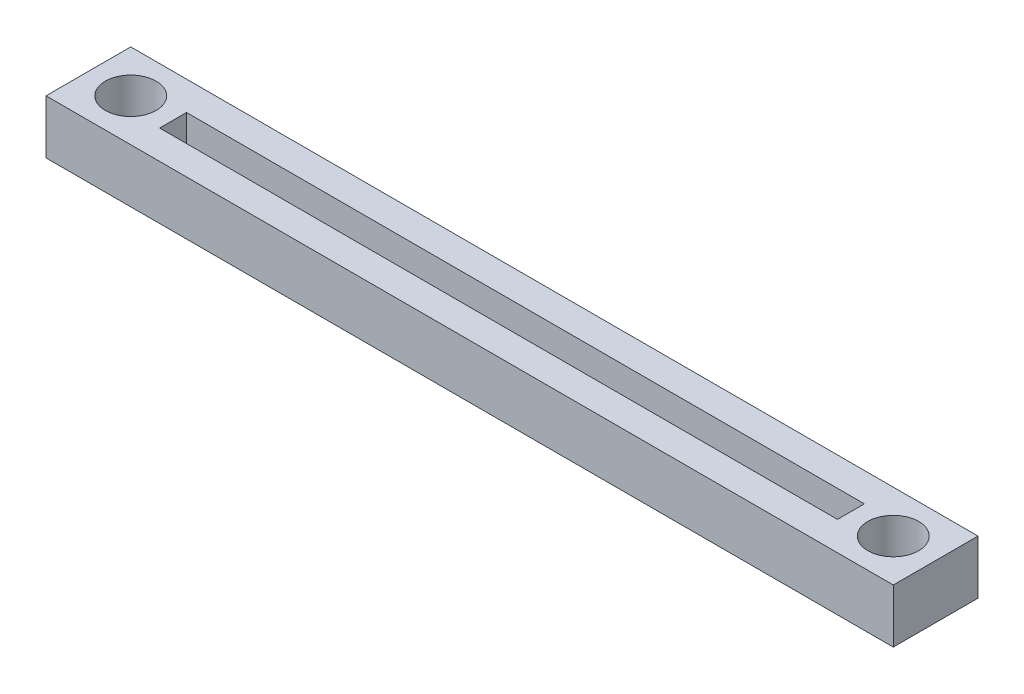
SolidWorks part; units mm, degrees
material "FiberBoard"
ref_plane "Front Plane" through (0, 0, 0) normal (0, 0, 1) x (1, 0, 0)
ref_plane "Top Plane" through (0, 0, 0) normal (0, 1, 0) x (1, 0, 0)
ref_plane "Right Plane" through (0, 0, 0) normal (1, 0, 0) x (0, 0, -1)
sketch "Sketch1" plane through (0, 0, 0) normal (0, 1, 0) x (1, 0, 0)
  line L1 (-50, 5) -> (50, 5)
  line L2 (-50, 5) -> (-50, -5)
  line L3 (-50, -5) -> (50, -5)
  line L4 (50, 5) -> (50, -5)
  line L5 (-50, 5) -> (50, -5) construction
  line L6 (-50, -5) -> (50, 5) construction
  point P0 (0, 0)
  dimension "D1" = 100
  dimension "D2" = 10
extrude "Boss-Extrude1" add sketch "Sketch1" along normal blind 6.35
sketch "Sketch2" plane through (0, 6.35, 0) normal (0, 1, 0) x (1, 0, 0)
  line L1 (-40, 1.5875) -> (40, 1.5875)
  line L2 (-40, 1.5875) -> (-40, -1.5875)
  line L3 (-40, -1.5875) -> (40, -1.5875)
  line L4 (40, 1.5875) -> (40, -1.5875)
  line L5 (-40, 1.5875) -> (40, -1.5875) construction
  line L6 (-40, -1.5875) -> (40, 1.5875) construction
  point P0 (0, 0)
  dimension "D1" = 80
  dimension "D2" = 3.175
extrude "Cut-Extrude1" cut sketch "Sketch2" against normal blind 6.35
hole_wizard "Ø6.0mm Dowel Hole1" positions "Sketch5" profile "Sketch4" hole size "Ø6.0" standard "ANSI Metric"
sketch "Sketch5" plane through (0, 6.35, 0) normal (0, 1, 0) x (1, 0, 0)
  line L0 (-50, 5) -> (-50, -5) construction
  line L1 (50, -5) -> (50, 5) construction
  line L2 (50, 5) -> (-50, 5) construction
  point P0 (-45, 0)
  point P2 (45, 0)
  dimension "D1" = 5
  dimension "D2" = 5
  dimension "D3" = 5
sketch "Sketch4" plane through (-45, 6.35, 0) normal (1, 0, 0) x (0, 0, 1)
  line L0 (0, 0) -> (0, 21.8026)
  line L1 (0, 21.8026) -> (3, 20)
  line L2 (3, 20) -> (3, 0)
  line L5 (3, 0) -> (0, 0)
  line L10 (0, 21.8026) -> (-3, 20) construction
  line L11 (0, -6.35) -> (0, 107.95) construction
  dimension "Hole Dia." = 6
  dimension "Hole Depth" = 20
  dimension "Drill Angle" = 118
